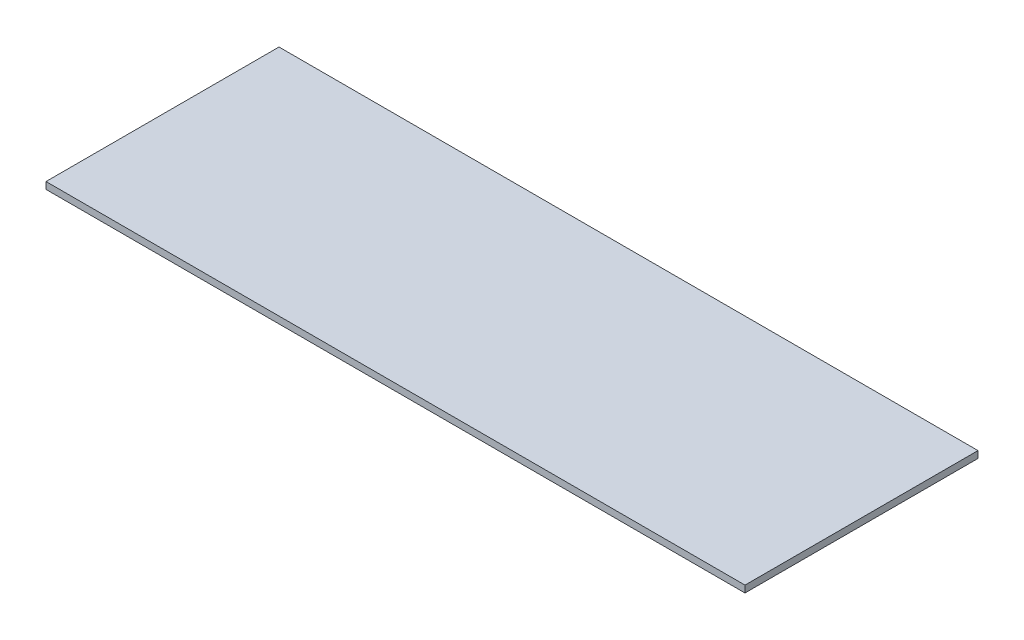
SolidWorks part; units mm, degrees
ref_plane "Front" through (0, 0, 0) normal (0, 0, 1) x (1, 0, 0)
ref_plane "Top" through (0, 0, 0) normal (0, 1, 0) x (1, 0, 0)
ref_plane "Right" through (0, 0, 0) normal (1, 0, 0) x (0, 0, -1)
sketch "Sketch1" plane through (0, 0, 0) normal (0, 0, 1) x (1, 0, 0)
  line L1 (0, 0) -> (-51, 0)
  line L2 (0, 0) -> (0, -0.5)
  line L3 (0, -0.5) -> (-51, -0.5)
  line L4 (-51, 0) -> (-51, -0.5)
  dimension "D1" = 51
  dimension "D2" = 0.5
extrude "Boss-Extrude1" add sketch "Sketch1" along normal blind 17
